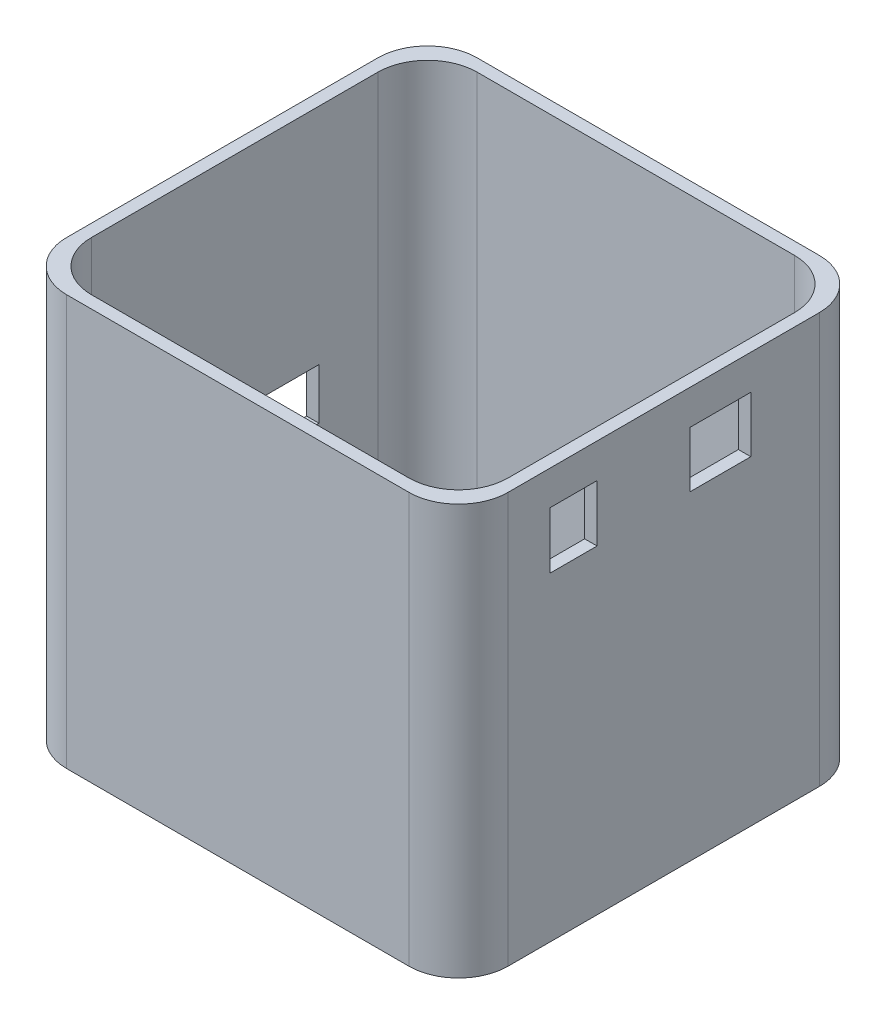
SolidWorks part; units mm, degrees
ref_plane "Front Plane" through (0, 0, 0) normal (0, 0, 1) x (1, 0, 0)
ref_plane "Top Plane" through (0, 0, 0) normal (0, 1, 0) x (1, 0, 0)
ref_plane "Right Plane" through (0, 0, 0) normal (1, 0, 0) x (0, 0, -1)
sketch "Sketch1" plane through (0, 0, 0) normal (0, 1, 0) x (1, 0, 0)
  line L1 (-45.212, -42.037) -> (45.212, -42.037)
  line L2 (-45.212, -42.037) -> (-45.212, 42.037)
  line L3 (-45.212, 42.037) -> (45.212, 42.037)
  line L4 (45.212, -42.037) -> (45.212, 42.037)
  line L5 (-45.212, -42.037) -> (45.212, 42.037) construction
  line L6 (-45.212, 42.037) -> (45.212, -42.037) construction
  point P0 (0, 0)
extrude "Boss-Extrude1" add sketch "Sketch1" along normal blind 84.074
sketch "Sketch3" plane through (0, 84.074, 0) normal (0, 1, 0) x (1, 0, 0)
  line L1 (-42.672, -39.497) -> (42.672, -39.497)
  line L2 (-42.672, -39.497) -> (-42.672, 39.497)
  line L3 (-42.672, 39.497) -> (42.672, 39.497)
  line L4 (42.672, -39.497) -> (42.672, 39.497)
  line L5 (-42.672, -39.497) -> (42.672, 39.497) construction
  line L6 (-42.672, 39.497) -> (42.672, -39.497) construction
  point P0 (0, 0)
extrude "Cut-Extrude1" cut sketch "Sketch3" against normal blind 81.534
sketch "Sketch5" plane through (-45.212, 0, 0) normal (-1, 0, 0) x (0, 0, 1)
  line L0 (-42.037, 84.074) -> (42.037, 84.074) construction
  line L1 (-17.272, 27.813) -> (17.272, 27.813)
  line L2 (-17.272, 27.813) -> (-17.272, 38.227)
  line L3 (-17.272, 38.227) -> (17.272, 38.227)
  line L4 (17.272, 27.813) -> (17.272, 38.227)
  line L5 (-17.272, 27.813) -> (17.272, 38.227) construction
  line L6 (-17.272, 38.227) -> (17.272, 27.813) construction
  point P0 (0, 33.02)
  dimension "D1" = 51.054
extrude "Cut-Extrude3" cut sketch "Sketch5" against normal blind 7.62
fillet "Fillet1" radius 10.16 8 edges at (-42.672, 43.307, -39.497) (42.672, 43.307, 39.497) (-42.672, 43.307, 39.497) (42.672, 43.307, -39.497) (45.212, 42.037, 42.037) (45.212, 42.037, -42.037) (-45.212, 42.037, -42.037) (-45.212, 42.037, 42.037)
sketch "Sketch6" plane through (45.212, 0, 0) normal (1, 0, 0) x (0, 0, -1)
  line L0 (-31.877, 84.074) -> (31.877, 84.074) construction
  line L1 (42.037, 84.074) -> (42.037, 0) construction
  line L3 (-23.3034, 77.0442) -> (-13.6514, 77.0442)
  line L4 (-23.3034, 77.0442) -> (-23.3034, 65.4357)
  line L5 (-23.3034, 65.4357) -> (-13.6514, 65.4357)
  line L6 (-13.6514, 77.0442) -> (-13.6514, 65.4357)
  line L7 (5.3983, 76.9622) -> (17.8443, 76.9622)
  line L8 (5.3983, 76.9622) -> (5.3983, 65.5322)
  line L9 (5.3983, 65.5322) -> (17.8443, 65.5322)
  line L10 (17.8443, 76.9622) -> (17.8443, 65.5322)
  point P0 (17.78, 76.962)
  point P5 (5.3983, 76.9622)
  point P6 (17.8443, 65.5322)
  point P7 (5.334, 65.532)
  point P8 (5.3983, 76.9622)
  point P9 (5.334, 65.532)
  point P10 (-13.6517, 76.9687)
  point P11 (-23.3034, 77.0442)
  point P12 (-13.6514, 65.4357)
  point P13 (-23.3037, 65.3602)
  dimension "D1" = 7.112
  dimension "D2" = 24.257
  dimension "D3" = 11.43
  dimension "D4" = 11.43
  dimension "D5" = 12.446
  dimension "D7" = 19.05
  dimension "D8" = 9.652
  dimension "D9" = 9.652
  dimension "D10" = 11.684
extrude "Cut-Extrude4" cut sketch "Sketch6" against normal blind 5.08
